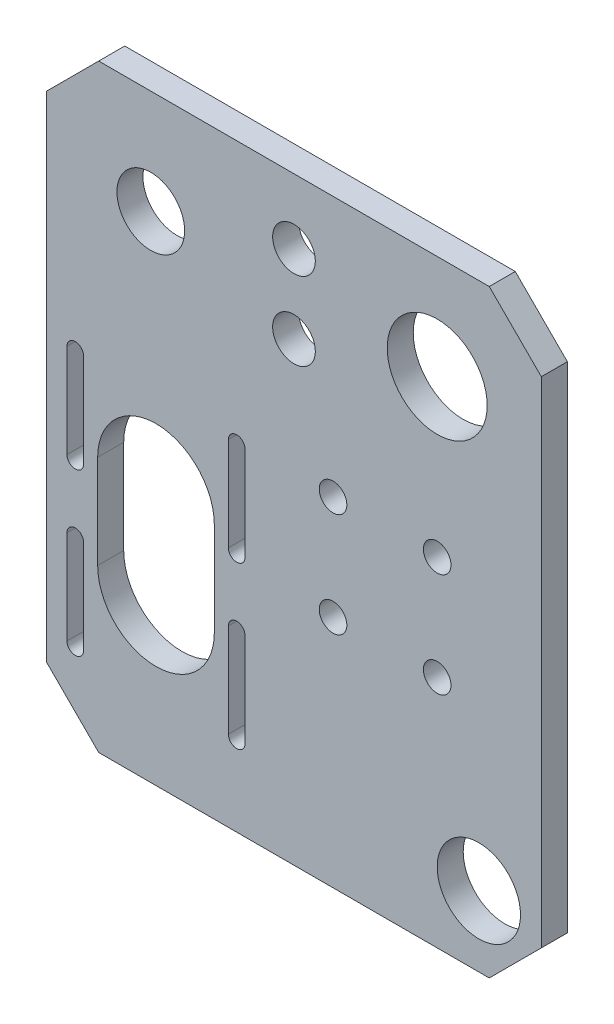
SolidWorks part; units mm, degrees
material "5052-O"
ref_plane "前基準面" through (0, 0, 0) normal (0, 0, 1) x (1, 0, 0)
ref_plane "上基準面" through (0, 0, 0) normal (0, 1, 0) x (1, 0, 0)
ref_plane "右基準面" through (0, 0, 0) normal (1, 0, 0) x (0, 0, -1)
sketch "草圖1" plane through (0, 0, 0) normal (0, 0, 1) x (1, 0, 0)
  line L1 (-47.5, -37.5) -> (47.5, -37.5)
  line L2 (-47.5, -37.5) -> (-47.5, 37.5)
  line L3 (-47.5, 37.5) -> (47.5, 37.5)
  line L4 (47.5, -37.5) -> (47.5, 37.5)
  line L5 (-47.5, -37.5) -> (47.5, 37.5) construction
  line L6 (-47.5, 37.5) -> (47.5, -37.5) construction
  point P0 (0, 0)
  dimension "D1" = 95
  dimension "D2" = 75
extrude "填料-伸長1" add sketch "草圖1" along normal blind 5
hole_wizard "M5 餘隙孔1" positions "草圖2" profile "草圖3" hole size "M5" standard "Ansi Metric" end condition through all
sketch "草圖2" plane through (0, 0, 5) normal (0, 0, 1) x (1, 0, 0)
  line L3 (7.5, 7.5) -> (27.5, 7.5) construction
  line L4 (7.5, 7.5) -> (7.5, 27.5) construction
  line L5 (7.5, 27.5) -> (27.5, 27.5) construction
  line L6 (27.5, 7.5) -> (27.5, 27.5) construction
  line L7 (7.5, 7.5) -> (27.5, 27.5) construction
  line L8 (7.5, 27.5) -> (27.5, 7.5) construction
  line L11 (47.5, 37.5) -> (-47.5, 37.5) construction
  line L12 (47.5, -37.5) -> (47.5, 37.5) construction
  point P6 (27.5, 27.5)
  point P15 (7.5, 7.5)
  point P16 (7.5, 27.5)
  point P17 (27.5, 7.5)
  point P35 (17.5, 17.5)
  dimension "D1" = 20
  dimension "D2" = 20
  dimension "D3" = 20
  dimension "D4" = 20
sketch "草圖3" plane through (27.5, 27.5, 5) normal (1, 0, 0) x (0, -1, 0)
  line L0 (0, 0) -> (0, 5)
  line L1 (0, 5) -> (2.65, 5)
  line L2 (2.65, 5) -> (2.65, 0)
  line L5 (2.65, 0) -> (0, 0)
  line L11 (0, -6.35) -> (0, 107.95) construction
  dimension "貫穿孔直徑" = 5.3
  dimension "貫穿孔深度" = 5
sketch "草圖6" plane through (0, 0, 5) normal (0, 0, 1) x (1, 0, 0)
  line L0 (47.5, 37.5) -> (-47.5, 37.5) construction
  line L2 (-26.5, -6.5) -> (-26.5, 11.5) construction
  line L3 (-37.7, -6.5) -> (-37.7, 11.5)
  line L4 (-15.3, -6.5) -> (-15.3, 11.5)
  line L6 (-42, 27) -> (-42, 9) construction
  line L7 (-42, -4) -> (-11, -4) construction
  line L8 (-42, -4) -> (-42, 27) construction
  line L9 (-42, 27) -> (-11, 27) construction
  line L10 (-11, -4) -> (-11, 27) construction
  line L11 (-42, -4) -> (-11, 27) construction
  line L12 (-42, 27) -> (-11, -4) construction
  line L13 (-40.4, 27) -> (-40.4, 9)
  line L14 (-43.6, 27) -> (-43.6, 9)
  line L15 (-11, 27) -> (-11, 9) construction
  line L16 (-9.4, 27) -> (-9.4, 9)
  line L17 (-12.6, 27) -> (-12.6, 9)
  line L18 (-11, -4) -> (-11, -22) construction
  line L19 (-9.4, -4) -> (-9.4, -22)
  line L20 (-12.6, -4) -> (-12.6, -22)
  line L21 (-42, -4) -> (-42, -22) construction
  line L22 (-40.4, -4) -> (-40.4, -22)
  line L23 (-43.6, -4) -> (-43.6, -22)
  line L25 (-47.5, 37.5) -> (-47.5, -37.5) construction
  arc A0 (-37.7, -6.5) -> (-15.3, -6.5) centre (-26.5, -6.5) ccw
  arc A1 (-15.3, 11.5) -> (-37.7, 11.5) centre (-26.5, 11.5) ccw
  arc A2 (-40.4, 27) -> (-43.6, 27) centre (-42, 27) ccw
  arc A3 (-43.6, 9) -> (-40.4, 9) centre (-42, 9) ccw
  arc A4 (-9.4, 27) -> (-12.6, 27) centre (-11, 27) ccw
  arc A5 (-12.6, 9) -> (-9.4, 9) centre (-11, 9) ccw
  arc A6 (-9.4, -4) -> (-12.6, -4) centre (-11, -4) ccw
  arc A7 (-12.6, -22) -> (-9.4, -22) centre (-11, -22) ccw
  arc A8 (-40.4, -4) -> (-43.6, -4) centre (-42, -4) ccw
  arc A9 (-43.6, -22) -> (-40.4, -22) centre (-42, -22) ccw
  point P6 (-26.5, 2.5)
  point P13 (-26.5, 11.5)
  point P18 (-42, 18)
  point P24 (-11, 18)
  point P30 (-11, -13)
  point P36 (-42, -13)
  dimension "D3" = 11.2
  dimension "D7" = 1.6
  dimension "D1" = 18
  dimension "D2" = 21
  dimension "D4" = 35
  dimension "D5" = 31
  dimension "D6" = 31
extrude "除料-伸長2" cut sketch "草圖6" against normal through all
sketch "草圖4" plane through (0, 0, 5) normal (0, 0, 1) x (1, 0, 0)
  circle A0 centre (35.5, -24) radius 8
  circle A1 centre (27.5, 7.5) radius 2.65 construction
  dimension "D3" = 16
  dimension "D1" = 31.5
  dimension "D2" = 8
extrude "除料-伸長3" cut sketch "草圖4" against normal up to next
sketch "草圖8" plane through (0, 37.5, 0) normal (0, 1, 0) x (1, 0, 0)
  line L1 (47.5, 0) -> (-47.5, 0)
  line L2 (47.5, 0) -> (47.5, -5)
  line L3 (47.5, -5) -> (-47.5, -5)
  line L4 (-47.5, 0) -> (-47.5, -5)
extrude "填料-伸長2" add sketch "草圖8" along normal blind 40
sketch "草圖9" plane through (0, 0, 5) normal (0, 0, 1) x (1, 0, 0)
  line L0 (47.5, -37.5) -> (47.5, 77.5) construction
  line L1 (-47.5, 77.5) -> (47.5, 77.5) construction
  circle A0 centre (27.5, 57.5) radius 9.6
  dimension "D1" = 19.2
  dimension "D3" = 20
  dimension "D2" = 20
extrude "除料-伸長4" cut sketch "草圖9" against normal up to next
sketch "草圖10" plane through (0, 0, 5) normal (0, 0, 1) x (1, 0, 0)
  line L0 (-47.5, 77.5) -> (47.5, 77.5) construction
  circle A0 centre (0, 65) radius 4.1
  circle A1 centre (0, 50) radius 4.1
  point P4 (0, 0)
  point P6 (0, 67.1978)
  dimension "D1" = 8.2
  dimension "D2" = 8.2
  dimension "D4" = 12.5
  dimension "D3" = 15
extrude "除料-伸長5" cut sketch "草圖10" against normal up to next
sketch "草圖11" plane through (0, 0, 5) normal (0, 0, 1) x (1, 0, 0)
  line L0 (-47.5, 77.5) -> (-47.5, -37.5) construction
  line L1 (-47.5, 77.5) -> (47.5, 77.5) construction
  circle A0 centre (-27.5, 57.5) radius 6.5
  dimension "D1" = 20
  dimension "D2" = 20
  dimension "D3" = 13
extrude "除料-伸長6" cut sketch "草圖11" against normal up to next
chamfer "導角2" distance 10 angle 45 4 edges at (47.5, -37.5, 2.5) (-47.5, -37.5, 2.5) (-47.5, 77.5, 2.5) (47.5, 77.5, 2.5)
